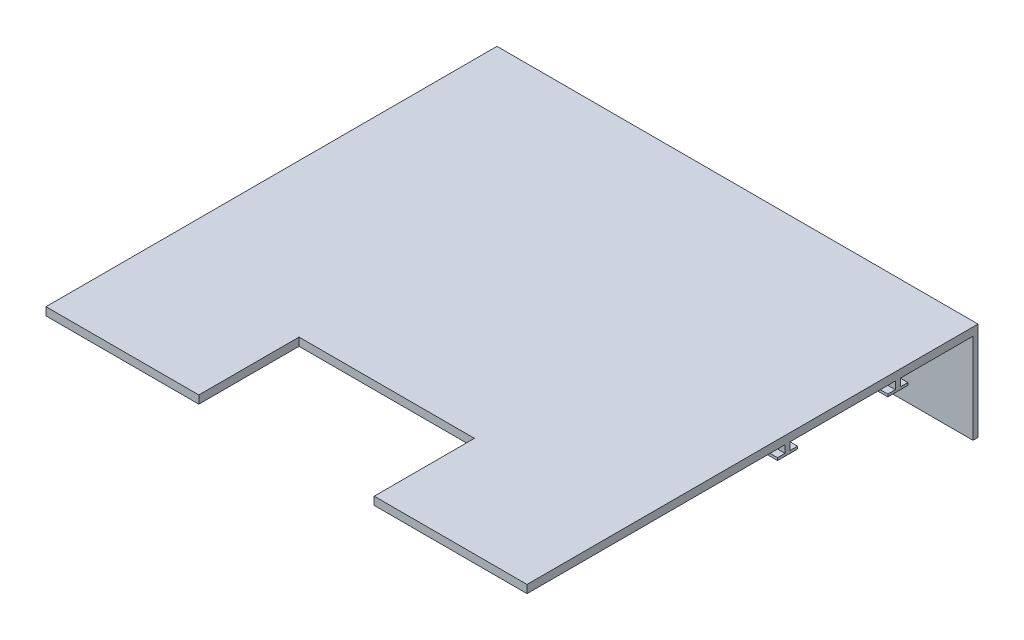
SolidWorks part; units mm, degrees
ref_plane "Front Plane" through (0, 0, 0) normal (0, 0, 1) x (1, 0, 0)
ref_plane "Top Plane" through (0, 0, 0) normal (0, 1, 0) x (1, 0, 0)
ref_plane "Right Plane" through (0, 0, 0) normal (1, 0, 0) x (0, 0, -1)
sketch "Sketch1" plane through (0, 0, 0) normal (0, 1, 0) x (1, 0, 0)
  line L1 (0, 0) -> (480, 0)
  line L2 (0, 0) -> (0, 450)
  line L3 (0, 450) -> (480, 450)
  line L4 (480, 0) -> (480, 450)
  dimension "D1" = 480
  dimension "D2" = 450
extrude "Boss-Extrude1" add sketch "Sketch1" along normal blind 8
sketch "Sketch2" plane through (0, 8, 0) normal (0, 1, 0) x (1, 0, 0)
  line L0 (240, -28.2037) -> (240, 169.1617) construction
  line L2 (152.5, 0) -> (327.5, 0)
  line L3 (152.5, 0) -> (152.5, 100)
  line L4 (152.5, 100) -> (327.5, 100)
  line L5 (327.5, 0) -> (327.5, 100)
  line L6 (0, 0) -> (480, 0) construction
  point P8 (240, 0)
  dimension "D1" = 175
  dimension "D2" = 100
extrude "Cut-Extrude1" cut sketch "Sketch2" against normal blind 10
sketch "Sketch4" plane through (0, 0, 0) normal (0, -1, 0) x (1, 0, 0)
  line L0 (0, -450) -> (0, 0) construction
  line L1 (480, -450) -> (0, -450) construction
  line L2 (240, -100) -> (240, -477.0808) construction
  line L4 (152.5, -100) -> (327.5, -100) construction
  line L5 (480, 0) -> (480, -450) construction
  circle A0 centre (30, -217) radius 3.5
  circle A1 centre (450, -217) radius 3.5
  dimension "D1" = 7
  dimension "D2" = 30
  dimension "D3" = 233
extrude "Boss-Extrude3" add sketch "Sketch4" along normal blind 15
sketch "Sketch5" plane through (0, 0, 0) normal (0, -1, 0) x (1, 0, 0)
  line L35 (5, -445) -> (0, -445)
  line L36 (0, -450) -> (0, 0) construction
  line L37 (480, -450) -> (0, -450)
  line L38 (0, -445) -> (0, -450)
  line L39 (475, -445) -> (480, -445)
  line L40 (480, 0) -> (480, -450) construction
  line L41 (480, -445) -> (480, -450)
  line L47 (475, -445) -> (5, -445)
  line L57 (475, -5) -> (475, -445) construction
  line L58 (480, 0) -> (480, -450) construction
  line L59 (327.5, 0) -> (480, 0) construction
  line L60 (327.5, -5) -> (475, -5) construction
  line L61 (0, 0) -> (152.5, 0) construction
  line L62 (5, -5) -> (152.5, -5) construction
  line L63 (5, -445) -> (5, -5) construction
  line L64 (0, -450) -> (0, 0) construction
  dimension "D2" = 5
extrude "Boss-Extrude4" add sketch "Sketch5" along normal blind 90
ref_plane "Plane2" through (0, 0, -315) normal (0, 0, 1) x (1, 0, 0)
sketch "Sketch9" plane through (0, 0, 0) normal (0, -1, 0) x (1, 0, 0)
  line L0 (0, -445) -> (0, 0) construction
  line L1 (0, -367.5) -> (480, -367.5)
  line L2 (0, -367.5) -> (0, -372.5)
  line L3 (0, -372.5) -> (480, -372.5)
  line L4 (480, -367.5) -> (480, -372.5)
  line L5 (480, 0) -> (480, -445) construction
  line L7 (0, -370) -> (491.4988, -370) construction
  line L8 (49.5, -315) -> (-49.5, -315) construction
  dimension "D1" = 55
  dimension "D2" = 5
extrude "Boss-Extrude6" add sketch "Sketch9" along normal blind 7.5
sketch "Sketch10" plane through (0, -7.5, 0) normal (0, -1, 0) x (1, 0, 0)
  line L2 (480, -360) -> (0, -360)
  line L3 (480, -360) -> (0, -360)
  line L4 (0, -360) -> (0, -380)
  line L5 (0, -380) -> (480, -380)
  line L6 (0, -380) -> (480, -380)
  line L7 (480, -360) -> (480, -380)
  dimension "D1" = 7.5
  dimension "D2" = 7.5
extrude "Boss-Extrude7" add sketch "Sketch10" along normal blind 2.5
mirror "Mirror9" about plane through (0, 0, -315) normal (0, 0, 1) of "Boss-Extrude6", "Boss-Extrude7"
ref_plane "Plane1" through (240, 0, 0) normal (1, 0, 0) x (0, 0, -1)
